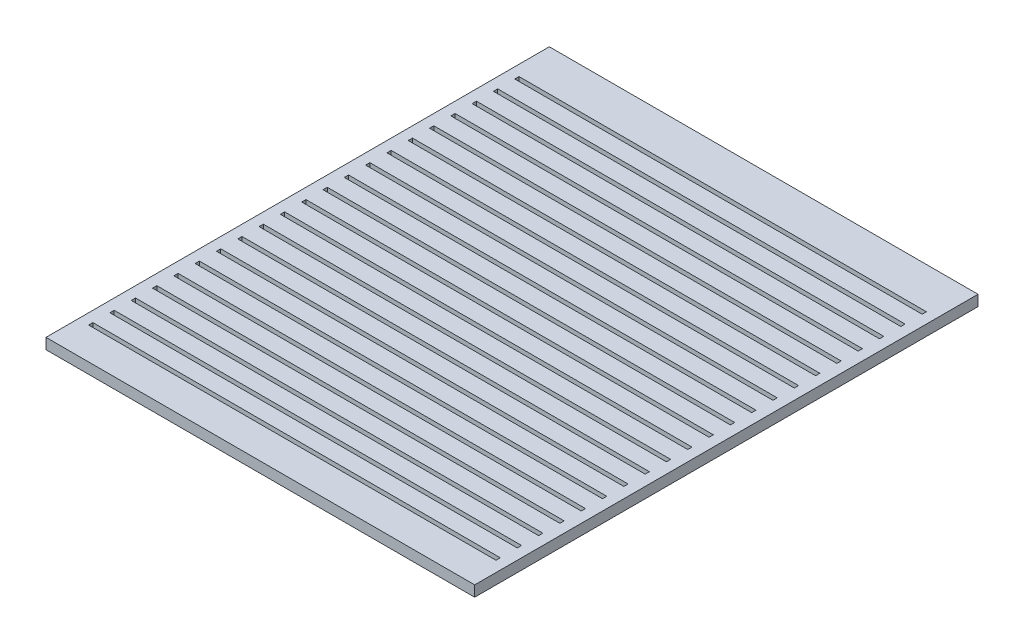
SolidWorks part; units mm, degrees
ref_plane "Front Plane" through (0, 0, 0) normal (0, 0, 1) x (1, 0, 0)
ref_plane "Top Plane" through (0, 0, 0) normal (0, 1, 0) x (1, 0, 0)
ref_plane "Right Plane" through (0, 0, 0) normal (1, 0, 0) x (0, 0, -1)
sketch "Sketch1" plane through (0, 0, 0) normal (0, 1, 0) x (1, 0, 0)
  line L5 (-121.41, 143.65) -> (-121.41, -143.65)
  line L6 (127.76, 150) -> (-127.76, 150)
  line L14 (127.76, 150) -> (127.76, -150)
  line L15 (127.76, -150) -> (-127.76, -150)
  line L16 (-127.76, 150) -> (-127.76, -150)
  line L17 (127.76, 150) -> (-127.76, -150) construction
  line L18 (127.76, -150) -> (-127.76, 150) construction
  line L19 (121.41, -143.65) -> (-121.41, -143.65)
  line L20 (121.41, 143.65) -> (121.41, -143.65)
  line L21 (121.41, 143.65) -> (-121.41, 143.65)
  point P0 (0, 0)
  dimension "D1" = 300
  dimension "D2" = 255.52
  dimension "D3" = 6.35
extrude "Boss-Extrude1" add sketch "Sketch1" against normal blind 6.35 contours L20 L21 L5 L19
sketch "Sketch4" plane through (0, 0, 0) normal (0, 1, 0) x (1, 0, 0)
  line L1 (127.76, 150) -> (-127.76, 150)
  line L2 (127.76, 150) -> (127.76, -150)
  line L3 (127.76, -150) -> (-127.76, -150)
  line L4 (-127.76, 150) -> (-127.76, -150)
  line L5 (127.76, 150) -> (-127.76, -150) construction
  line L6 (127.76, -150) -> (-127.76, 150) construction
  point P4 (0, 0)
extrude "Boss-Extrude4" add sketch "Sketch4" along normal blind 6.4008
sketch "Sketch5" plane through (0, -6.35, 0) normal (0, -1, 0) x (1, 0, 0)
  line L0 (-121.41, -143.65) -> (-121.41, 143.65) construction
  line L1 (-121.41, 130.95) -> (121.41, 130.95)
  line L2 (-121.41, 130.95) -> (-121.41, 128.41)
  line L3 (-121.41, 128.41) -> (121.41, 128.41)
  line L4 (121.41, 130.95) -> (121.41, 128.41)
  line L5 (-121.41, 130.95) -> (121.41, 128.41) construction
  line L6 (-121.41, 128.41) -> (121.41, 130.95) construction
  line L7 (121.41, -143.65) -> (121.41, 143.65) construction
  line L8 (121.41, 143.65) -> (-121.41, 143.65) construction
  point P4 (0, 129.68)
  dimension "D1" = 2.54
  dimension "D2" = 12.7
extrude "Boss-Extrude5" add sketch "Sketch5" against normal blind 49.5808 separate body
pattern_linear "LPattern1" count 21 spacing 12.7 along (0, 0, -1) of "Boss-Extrude5"
combine bodies "Combine1" operation type subtract main body 104 bodies to subtract 105 106 107 108 110 111 109 112 113 115 116 114 117 121 123 125 124 122 120 119 118
